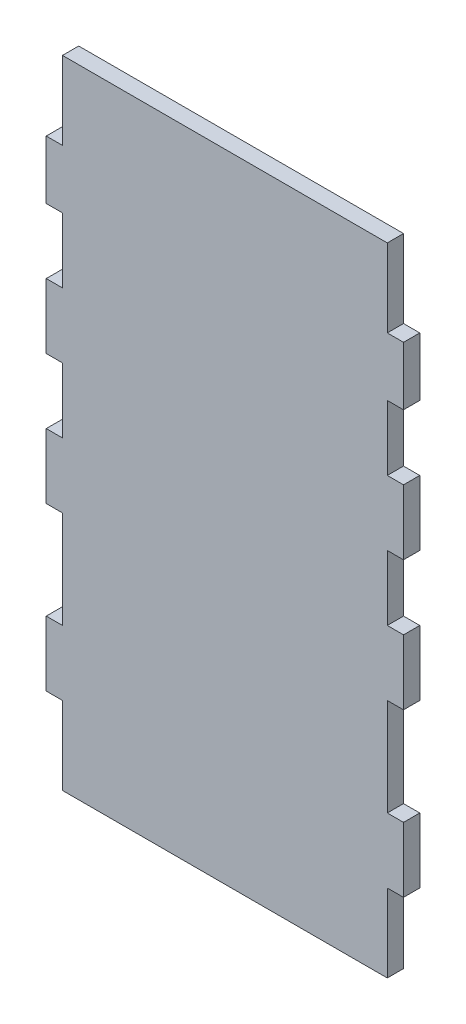
SolidWorks part; units mm, degrees
ref_plane "Front Plane" through (0, 0, 0) normal (0, 0, 1) x (1, 0, 0)
ref_plane "Top Plane" through (0, 0, 0) normal (0, 1, 0) x (1, 0, 0)
ref_plane "Right Plane" through (0, 0, 0) normal (1, 0, 0) x (0, 0, -1)
sketch "Sketch1" plane through (0, 0, 0) normal (0, 0, 1) x (1, 0, 0)
  line L0 (-190.5, 252.73) -> (-209.55, 252.73) construction
  line L1 (6.35, 6.35) -> (-133.35, 6.35)
  line L2 (6.35, 6.35) -> (6.35, 252.73)
  line L3 (6.35, 252.73) -> (-133.35, 252.73)
  line L4 (-133.35, 6.35) -> (-133.35, 252.73)
  line L5 (-127, 1.27) -> (-127, 6.35) construction
  dimension "D1" = 6.35
extrude "Boss-Extrude1" add sketch "Sketch1" along normal blind 6.35
sketch "Sketch2" plane through (6.35, 0, 0) normal (1, 0, 0) x (0, 0, -1)
  line L0 (0, 6.35) -> (0, 252.73) construction
  line L1 (-6.35, 6.35) -> (0, 6.35)
  line L2 (-6.35, 6.35) -> (-6.35, 33.02)
  line L3 (-6.35, 33.02) -> (0, 33.02)
  line L4 (0, 6.35) -> (0, 33.02)
  line L5 (-6.35, 6.35) -> (-6.35, 252.73) construction
  line L6 (-6.35, 58.42) -> (0, 58.42)
  line L7 (-6.35, 58.42) -> (-6.35, 96.52)
  line L8 (-6.35, 96.52) -> (0, 96.52)
  line L9 (0, 58.42) -> (0, 96.52)
  line L11 (-6.35, 121.92) -> (0, 121.92)
  line L12 (-6.35, 121.92) -> (-6.35, 147.32)
  line L13 (-6.35, 147.32) -> (0, 147.32)
  line L14 (0, 121.92) -> (0, 147.32)
  line L15 (-6.35, 172.72) -> (0, 172.72)
  line L16 (-6.35, 172.72) -> (-6.35, 198.12)
  line L17 (-6.35, 198.12) -> (0, 198.12)
  line L18 (0, 172.72) -> (0, 198.12)
  line L19 (0, 220.98) -> (-6.35, 220.98)
  line L20 (0, 220.98) -> (0, 252.73)
  line L21 (0, 252.73) -> (-6.35, 252.73)
  line L22 (-6.35, 220.98) -> (-6.35, 252.73)
  dimension "D1" = 26.67
  dimension "D2" = 25.4
  dimension "D3" = 38.1
  dimension "D4" = 25.4
  dimension "D5" = 25.4
  dimension "D6" = 25.4
  dimension "D7" = 25.4
  dimension "D8" = 22.86
  dimension "D9" = 31.75
extrude "Cut-Extrude1" cut sketch "Sketch2" against normal blind 6.35
sketch "Sketch6" plane through (0, 0, 0) normal (1, 0, 0) x (0, 0, -1)
  line L0 (-6.35, 252.73) -> (-6.35, 220.98) construction
  line L1 (0, 252.73) -> (-6.35, 252.73)
  line L2 (0, 252.73) -> (0, 251.46)
  line L3 (0, 251.46) -> (-6.35, 251.46)
  line L4 (-6.35, 252.73) -> (-6.35, 251.46)
  dimension "D1" = 1.27
sketch "Sketch7" plane through (0, 0, 0) normal (0, 0, -1) x (-1, 0, 0)
  line L0 (66.675, 6.35) -> (66.675, 59.8133) construction
  line L1 (133.35, 6.35) -> (0, 6.35) construction
  line L3 (63.5, 6.35) -> (63.5, 63.249) construction
  line L4 (127, 33.02) -> (127, 6.35)
  line L5 (133.35, 33.02) -> (127, 33.02)
  line L7 (127, 58.42) -> (133.35, 58.42)
  line L8 (127, 96.52) -> (127, 58.42)
  line L9 (133.35, 96.52) -> (127, 96.52)
  line L11 (127, 121.92) -> (133.35, 121.92)
  line L12 (127, 147.32) -> (127, 121.92)
  line L13 (133.35, 147.32) -> (127, 147.32)
  line L15 (127, 172.72) -> (133.35, 172.72)
  line L16 (127, 198.12) -> (127, 172.72)
  line L17 (133.35, 198.12) -> (127, 198.12)
  line L19 (127, 220.98) -> (133.35, 220.98)
  line L20 (127, 247.65) -> (127, 220.98)
  line L21 (127, 247.65) -> (127, 220.98)
  line L22 (127, 33.02) -> (127, 6.35)
  line L23 (127, 96.52) -> (127, 58.42)
  line L24 (127, 147.32) -> (127, 121.92)
  line L25 (127, 198.12) -> (127, 172.72)
  line L26 (127, 247.65) -> (127, 252.73)
  line L27 (0, 252.73) -> (133.35, 252.73) construction
  line L28 (127, 252.73) -> (133.35, 252.73)
  line L29 (133.35, 252.73) -> (133.35, 220.98)
  line L30 (133.35, 6.35) -> (127, 6.35)
  line L31 (133.35, 198.12) -> (133.35, 172.72)
  line L32 (133.35, 147.32) -> (133.35, 121.92)
  line L33 (133.35, 96.52) -> (133.35, 58.42)
  line L34 (133.35, 33.02) -> (133.35, 6.35)
  line M23 (133.35, 6.35) -> (133.35, 252.73)
  line M42 (0, 6.35) -> (133.35, 6.35)
  line M62 (133.35, 252.73) -> (0, 252.73)
  dimension "D2" = 3.175
extrude "Cut-Extrude5" cut sketch "Sketch7" against normal through all contours L5 L4 M23 M42 | L9 L8 L7 M23 | L13 L12 L11 M23 | L17 L16 L15 M23 | L26 L20 L19 M23 M62
sketch "Sketch8" plane through (0, 6.35, 0) normal (0, -1, 0) x (1, 0, 0)
  line L1 (-127, 6.35) -> (-127, 0)
  line L4 (-127, 0) -> (0, 0)
  line L5 (0, 0) -> (0, 6.35)
  line L6 (0, 6.35) -> (-127, 6.35)
  line L7 (-127, 6.35) -> (-127, 0)
  line L8 (-127, 0) -> (0, 0)
  line L9 (0, 0) -> (0, 6.35)
  line L10 (0, 6.35) -> (-127, 6.35)
  dimension "D1" = 0
extrude "Boss-Extrude2" add sketch "Sketch8" along normal blind 3.81
extrude "Cut-Extrude6" cut sketch "Sketch6" against normal through all
